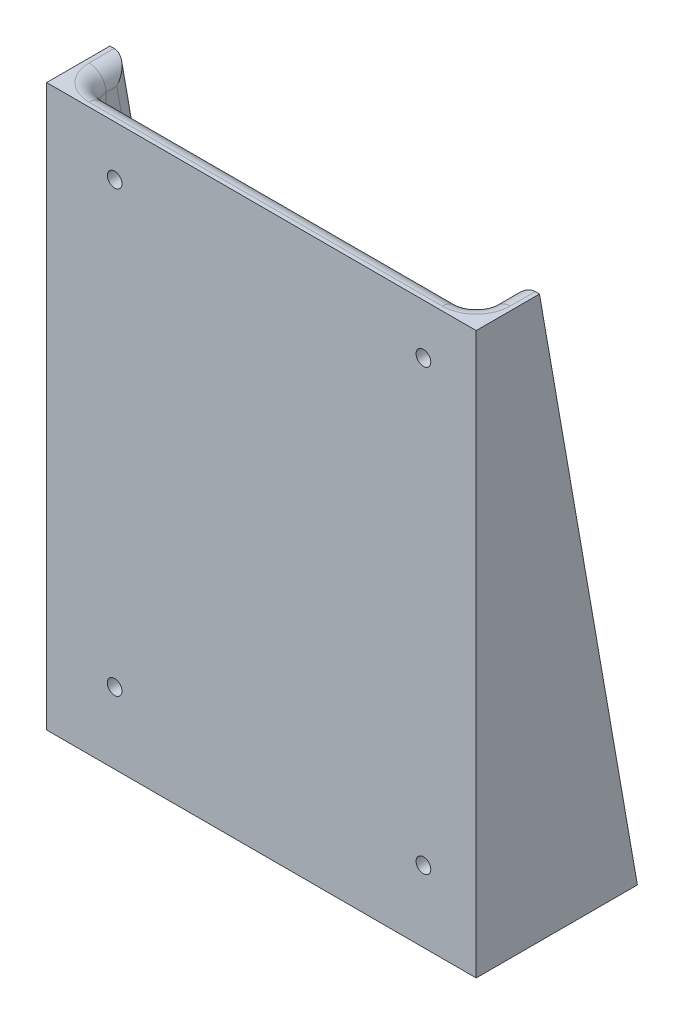
SolidWorks part; units mm, degrees
ref_plane "Front Plane" through (0, 0, 0) normal (0, 0, 1) x (1, 0, 0)
ref_plane "Top Plane" through (0, 0, 0) normal (0, 1, 0) x (1, 0, 0)
ref_plane "Right Plane" through (0, 0, 0) normal (1, 0, 0) x (0, 0, -1)
sketch "Sketch1" plane through (0, 0, 0) normal (1, 0, 0) x (0, 0, -1)
  line L0 (0, 0) -> (24.13, 0)
  line L2 (0, 83.947) -> (0, 0)
  line L3 (24.13, 0) -> (9.4742, 83.947)
  line L4 (9.4742, 83.947) -> (0, 83.947)
  dimension "D1" = 9.4742
  dimension "D2" = 83.947
  dimension "D3" = 24.13
extrude "Boss-Extrude1" add sketch "Sketch1" along normal mid plane 64.3128 contours L2 L0 L3 L4
sketch "Sketch2" plane through (0, 83.947, 0) normal (0, 1, 0) x (1, 0, 0)
  line L0 (-32.1564, 9.4742) -> (-32.1564, 0) construction
  line L1 (-28.9814, 3.175) -> (28.9814, 3.175)
  line L2 (-28.9814, 3.175) -> (-28.9814, 24.13)
  line L3 (-28.9814, 24.13) -> (28.9814, 24.13)
  line L4 (28.9814, 3.175) -> (28.9814, 24.13)
  line L5 (32.1564, 9.4742) -> (32.1564, 0) construction
  line L6 (32.1564, 0) -> (-32.1564, 0) construction
  line L7 (32.1564, 24.13) -> (-32.1564, 24.13) construction
  dimension "D1" = 3.175
  dimension "D2" = 3.175
  dimension "D3" = 3.175
extrude "Cut-Extrude1" cut sketch "Sketch2" against normal offset from surface (80.772 mm away) 3.175 up to face at (0, 0, -12.065)
hole_wizard "M2 Clearance Hole1" positions "Sketch3" profile "Sketch4" hole size "M2" standard "ANSI Metric" end condition through all
sketch "Sketch3" plane through (0, 0, 0) normal (0, 0, 1) x (1, 0, 0)
  point P0 (-21.971, 76.454)
  point P3 (24.257, 76.454)
  point P6 (24.257, 10.668)
  point P9 (-21.971, 10.668)
  point P17 (0, 0)
  dimension "D1" = 46.228
  dimension "D2" = 65.786
  dimension "D3" = 46.228
  dimension "D4" = 65.786
sketch "Sketch4" plane through (-21.971, 76.454, 0) normal (1, 0, 0) x (0, -1, 0)
  line L0 (0, 0) -> (0, 24.13)
  line L1 (0, 24.13) -> (1.1, 24.13)
  line L2 (1.1, 24.13) -> (1.1, 0)
  line L5 (1.1, 0) -> (0, 0)
  line L11 (0, -6.35) -> (0, 107.95) construction
  dimension "Thru Hole Dia." = 2.2
  dimension "Thru Hole Depth" = 24.13
hole_wizard "#2 (0.221) Diameter Hole1" positions "Sketch5" profile "Sketch6" hole size "#2" standard "ANSI Inch" end condition through all
sketch "Sketch5" plane through (0, 0, 0) normal (0, -1, 0) x (-1, 0, 0)
  line L0 (-32.1564, 12.065) -> (32.1564, 12.065)
  line L1 (-32.1564, 0) -> (-32.1564, 24.13) construction
  line L2 (32.1564, 0) -> (32.1564, 24.13) construction
  point P0 (-16.9164, 12.065)
  point P2 (16.9164, 12.065)
  dimension "D1" = 15.24
  dimension "D2" = 15.24
sketch "Sketch6" plane through (16.9164, 0, -12.065) normal (1, 0, 0) x (0, 0, -1)
  line L0 (0, 0) -> (0, 83.947)
  line L1 (0, 83.947) -> (2.8067, 83.947)
  line L2 (2.8067, 83.947) -> (2.8067, 0)
  line L5 (2.8067, 0) -> (0, 0)
  line L11 (0, -6.35) -> (0, 107.95) construction
  dimension "Thru Hole Dia." = 5.6134
  dimension "Thru Hole Depth" = 83.947
fillet "Fillet1" radius 2.54 11 edges at (28.9814, 43.561, -16.5249) (28.9814, 83.947, -6.3246) (0, 3.175, -23.5757) (0, 83.947, -3.175) (-28.9814, 43.561, -16.5249) (-28.9814, 3.175, -13.3753) (-28.9814, 83.947, -6.3246) (0, 3.175, -3.175) (28.9814, 3.175, -13.3753) (-28.9814, 43.561, -3.175) (28.9814, 43.561, -3.175)
